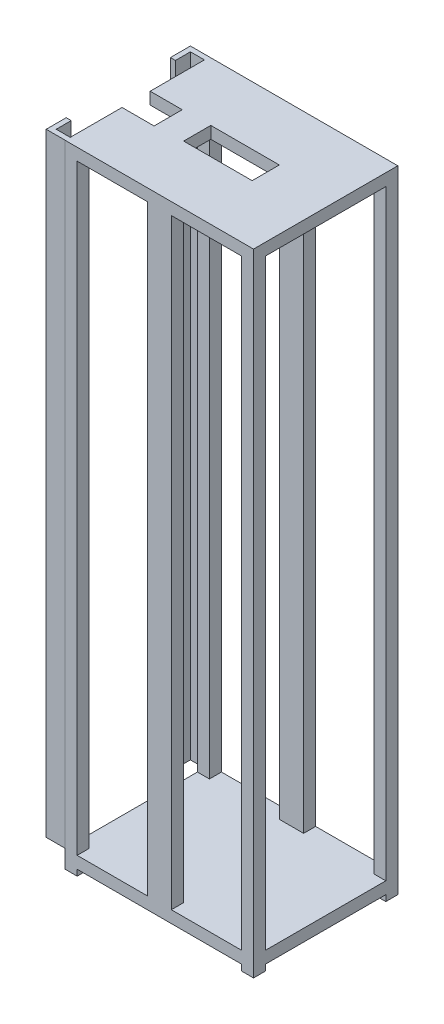
SolidWorks part; units mm, degrees
ref_plane "Front Plane" through (0, 0, 0) normal (0, 0, 1) x (1, 0, 0)
ref_plane "Top Plane" through (0, 0, 0) normal (0, 1, 0) x (1, 0, 0)
ref_plane "Right Plane" through (0, 0, 0) normal (1, 0, 0) x (0, 0, -1)
sketch "Sketch1" plane through (0, 0, 0) normal (0, 1, 0) x (1, 0, 0)
  line L1 (-470, 360) -> (470, 360)
  line L2 (-470, 360) -> (-470, -360)
  line L3 (-470, -360) -> (470, -360)
  line L4 (470, 360) -> (470, -360)
  line L5 (-470, 360) -> (470, -360) construction
  line L6 (-470, -360) -> (470, 360) construction
  point P0 (0, 0)
  dimension "D1" = 940
  dimension "D2" = 720
extrude "Boss-Extrude1" add sketch "Sketch1" along normal blind 60
sketch "Sketch2" plane through (0, 60, 0) normal (0, 1, 0) x (1, 0, 0)
  line L0 (0, 360) -> (0, -360) construction
  line L1 (-470, 360) -> (-410, 360)
  line L2 (-470, 360) -> (-470, 300)
  line L3 (-470, 300) -> (-410, 300)
  line L4 (-410, 360) -> (-410, 300)
  line L5 (470, 360) -> (-470, 360) construction
  line L6 (-470, -360) -> (470, -360) construction
  line L7 (-470, 0) -> (470, 0) construction
  line L8 (-470, 360) -> (-470, -360) construction
  line L9 (470, -360) -> (470, 360) construction
  line L10 (410, 360) -> (470, 360)
  line L11 (410, 360) -> (410, 300)
  line L12 (410, 300) -> (470, 300)
  line L13 (470, 360) -> (470, 300)
  line L14 (470, -360) -> (470, -300)
  line L15 (410, -300) -> (470, -300)
  line L16 (410, -360) -> (410, -300)
  line L17 (410, -360) -> (470, -360)
  line L18 (-410, -360) -> (-410, -300)
  line L19 (-470, -300) -> (-410, -300)
  line L20 (-470, -360) -> (-470, -300)
  line L21 (-470, -360) -> (-410, -360)
  point P29 (410, -330)
  dimension "D1" = 2
  dimension "D2" = 60
  dimension "D3" = 60
  dimension "D4" = 60
  dimension "D6" = 60
extrude "Boss-Extrude2" add sketch "Sketch2" along normal blind 3000
sketch "Sketch3" plane through (0, 0, 0) normal (0, -1, 0) x (1, 0, 0)
  line L1 (-470, 360) -> (-410, 360)
  line L2 (-470, 360) -> (-470, 300)
  line L3 (-470, 300) -> (-410, 300)
  line L4 (-410, 360) -> (-410, 300)
  line L5 (-470, -360) -> (-410, -360)
  line L6 (-470, -360) -> (-470, -300)
  line L7 (-470, -300) -> (-410, -300)
  line L8 (-410, -360) -> (-410, -300)
  line L9 (470, 360) -> (410, 360)
  line L10 (470, 360) -> (470, 300)
  line L11 (470, 300) -> (410, 300)
  line L12 (410, 360) -> (410, 300)
  line L13 (470, -360) -> (410, -360)
  line L14 (470, -360) -> (470, -300)
  line L15 (470, -300) -> (410, -300)
  line L16 (410, -360) -> (410, -300)
extrude "Boss-Extrude3" add sketch "Sketch3" along normal blind 30
ref_plane "Plane1" through (0, 3060, 0) normal (0, 1, 0) x (1, 0, 0)
sketch "Sketch4" plane through (0, 3060, 0) normal (0, 1, 0) x (1, 0, 0)
  line L1 (-470, 360) -> (470, 360)
  line L2 (-470, 360) -> (-470, -360)
  line L3 (-470, -360) -> (470, -360)
  line L4 (470, 360) -> (470, -360)
extrude "Boss-Extrude4" add sketch "Sketch4" along normal blind 60
sketch "Sketch5" plane through (0, 0, 0) normal (0, 1, 0) x (1, 0, 0)
  line L0 (0, 360) -> (0, -360) construction
  line L1 (470, 360) -> (-470, 360) construction
  line L2 (-470, -360) -> (470, -360) construction
  line L3 (-259.5501, 360) -> (-139.5501, 360) construction
  line L4 (-517, 0) -> (517, 0) construction
  line L5 (-60, 360) -> (60, 360)
  line L6 (-60, 360) -> (-60, 300)
  line L7 (-60, 300) -> (60, 300)
  line L8 (60, 360) -> (60, 300)
  line L9 (-60, 360) -> (60, 300) construction
  line L10 (-60, 300) -> (60, 360) construction
  line L11 (-60, -300) -> (60, -360) construction
  line L12 (-60, -360) -> (60, -300) construction
  line L13 (60, -360) -> (60, -300)
  line L14 (-60, -300) -> (60, -300)
  line L15 (-60, -360) -> (-60, -300)
  line L16 (-60, -360) -> (60, -360)
  point P8 (0, 330)
  point P19 (0, -330)
  dimension "D1" = 60
  dimension "D2" = 120
extrude "Boss-Extrude5" add sketch "Sketch5" along normal up to surface (3120 mm away) up to face at (0, 3120, 0)
sketch "Sketch6" plane through (0, 3120, 0) normal (0, 1, 0) x (1, 0, 0)
  line L1 (-170.979, 67.7884) -> (170.979, 67.7884)
  line L2 (-170.979, 67.7884) -> (-170.979, -67.7884)
  line L3 (-170.979, -67.7884) -> (170.979, -67.7884)
  line L4 (170.979, 67.7884) -> (170.979, -67.7884)
  line L5 (-170.979, 67.7884) -> (170.979, -67.7884) construction
  line L6 (-170.979, -67.7884) -> (170.979, 67.7884) construction
  point P0 (0, 0)
extrude "Cut-Extrude1" cut sketch "Sketch6" against normal up to surface (60 mm away) up to face at (0, 3060, 0)
sketch "Sketch8" plane through (0, 3060, 0) normal (0, -1, 0) x (1, 0, 0)
  line L0 (0, 360) -> (0, -360) construction
  line L1 (-410, 360) -> (410, 360) construction
  line L2 (410, -360) -> (-410, -360) construction
  line L3 (365, 29) -> (365, -77) construction
  circle A9 centre (365, 12) radius 17
  circle A10 centre (365, -60) radius 17
  circle A11 centre (365, -24) radius 17
  circle A12 centre (365, 12) radius 7
  circle A13 centre (365, -24) radius 7
  circle A14 centre (365, -60) radius 7
  dimension "D2" = 34
  dimension "D3" = 34
  dimension "D5" = 36
  dimension "D1" = 34
  dimension "D4" = 36
  dimension "D6" = 10
extrude "Boss-Extrude9" add sketch "Sketch8" along normal blind 70
sketch "Sketch13" plane through (0, 3120, 0) normal (0, 1, 0) x (1, 0, 0)
  line L0 (470, 360) -> (-470, 360) construction
  line L1 (-435.6836, 360) -> (-565, 360)
  line L2 (-435.6836, 360) -> (-435.6836, 335)
  line L3 (-435.6836, -359.539) -> (-565, -359.539)
  line L4 (-565, 360) -> (-565, 260)
  line L5 (-435.6836, -334.539) -> (-435.6836, -359.539)
  line L6 (-435.6836, 335) -> (-540, 335)
  line L8 (-435.6836, -334.539) -> (-540, -334.539)
  line L9 (-540, 335) -> (-540, 260)
  line L10 (-565, -259.539) -> (-565, -359.539)
  line L11 (-565, 260) -> (-540, 260)
  line L13 (-565, -259.539) -> (-540, -259.539)
  line L15 (-540, -259.539) -> (-540, -334.539)
  line L16 (-470, 360) -> (-470, -360) construction
  dimension "D1" = 25
  dimension "D2" = 25
  dimension "D3" = 25
  dimension "D4" = 100
  dimension "D5" = 100
  dimension "D6" = 70
  dimension "D7" = 70
  dimension "D8" = 669.539
extrude "Boss-Extrude10" add sketch "Sketch13" against normal up to surface (3060 mm away) up to face at (0, 60, 0)
sketch "Sketch14" plane through (0, 2990, 0) normal (0, -1, 0) x (1, 0, 0)
  circle A0 centre (365, 12) radius 7
  circle A1 centre (365, -24) radius 7
  circle A2 centre (365, -60) radius 7
sketch "Sketch15" plane through (0, 3120, 0) normal (0, 1, 0) x (1, 0, 0)
  line L0 (-470, 335) -> (-470, -334.539) construction
  line L1 (-470, 64.3142) -> (-310.0666, 64.3142)
  line L2 (-470, 64.3142) -> (-470, -76.1341)
  line L3 (-470, -76.1341) -> (-310.0666, -76.1341)
  line L4 (-310.0666, 64.3142) -> (-310.0666, -76.1341)
  line L5 (-170.979, -67.7884) -> (170.979, -67.7884) construction
  line L6 (170.979, 67.7884) -> (-170.979, 67.7884) construction
extrude "Cut-Extrude2" cut sketch "Sketch15" against normal up to surface (60 mm away) up to face at (365, 3060, -7)
